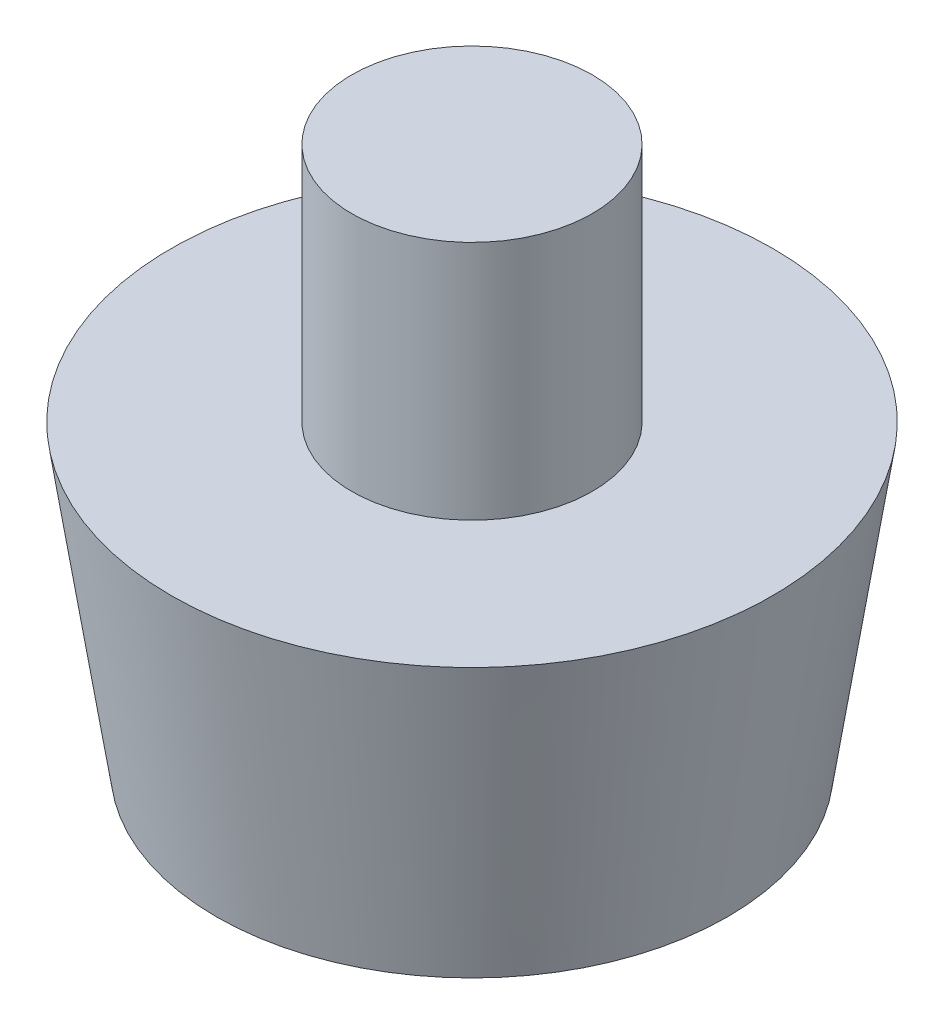
SolidWorks part; units mm, degrees
ref_plane "Front Plane" through (0, 0, 0) normal (0, 0, 1) x (1, 0, 0)
ref_plane "Top Plane" through (0, 0, 0) normal (0, 1, 0) x (1, 0, 0)
ref_plane "Right Plane" through (0, 0, 0) normal (1, 0, 0) x (0, 0, -1)
sketch "Sketch1" plane through (0, 0, 0) normal (0, 0, 1) x (1, 0, 0)
  line L0 (0, 0) -> (0, 18) construction
  line L1 (0, 2) -> (-3, 2)
  line L2 (-3, 2) -> (-3, 4.5)
  line L3 (-3, 4.5) -> (-4, 4.5)
  line L4 (-4, 4.5) -> (-4, 0)
  line L5 (-4, 0) -> (-8.5, 0)
  line L6 (-8.5, 0) -> (-10, 10)
  line L7 (-10, 10) -> (-4, 10)
  line L8 (-4, 10) -> (-4, 18)
  line L9 (-4, 18) -> (0, 18)
  line L10 (0, 2) -> (0, 18)
  dimension "D1" = 8.5
  dimension "D2" = 10
  dimension "D3" = 2
  dimension "D4" = 3
  dimension "D5" = 1
  dimension "D6" = 2.5
  dimension "D7" = 8
  dimension "D8" = 10
  dimension "D9" = 8
revolve "Revolve1" add sketch "Sketch1" angle 360 about L0
